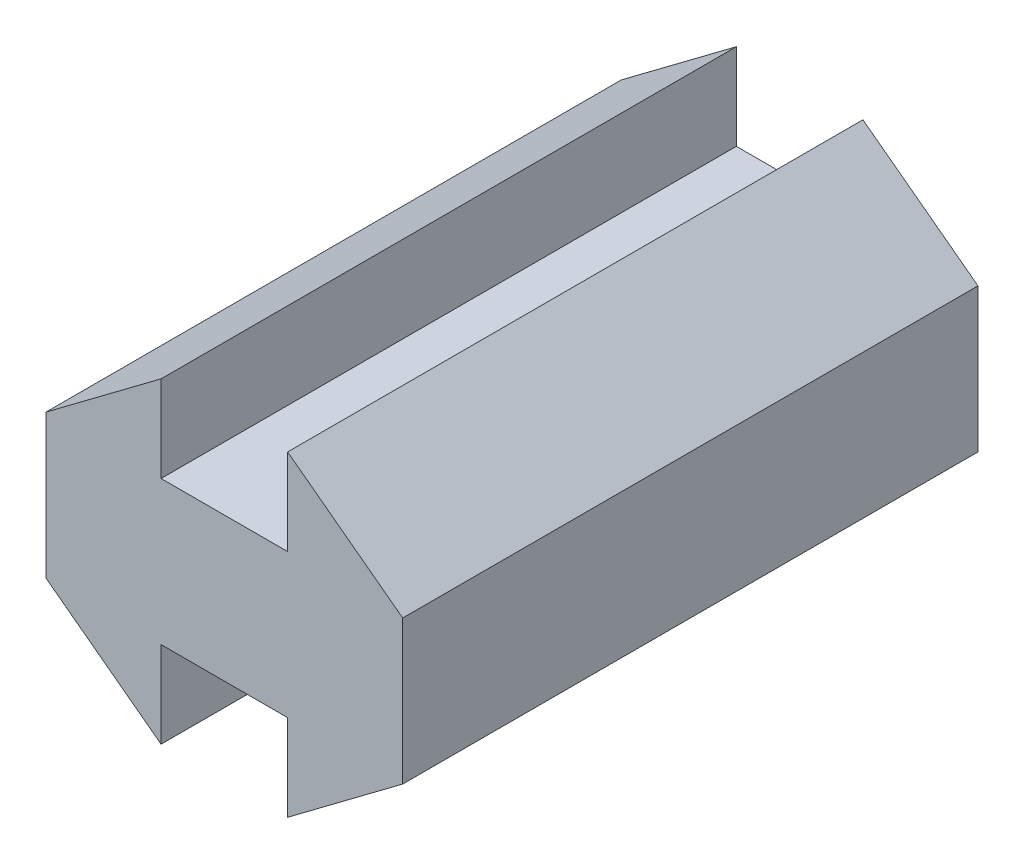
SolidWorks part; units mm, degrees
ref_plane "Plan de face" through (0, 0, 0) normal (0, 0, 1) x (1, 0, 0)
ref_plane "Plan de dessus" through (0, 0, 0) normal (0, 1, 0) x (1, 0, 0)
ref_plane "Plan de droite" through (0, 0, 0) normal (1, 0, 0) x (0, 0, -1)
sketch "ProfileRainureEsquisse" plane through (0, 0, 0) normal (0, 0, 1) x (1, 0, 0)
  line L0 (0, 0) -> (0, 5)
  line L1 (0, 5) -> (4, 8)
  line L2 (0, 0) -> (4, -3)
  line L3 (4, 8) -> (4, 5)
  line L4 (4, 5) -> (8.4, 5)
  line L5 (8.4, 0) -> (8.4, -3)
  line L6 (8.4, 0) -> (4, 0)
  line L7 (4, 0) -> (4, -3)
  line L8 (8.4, 5) -> (8.4, 8)
  line L11 (8.4, 8) -> (12.4, 5)
  line L12 (12.4, 5) -> (12.4, 0)
  line L13 (12.4, 0) -> (8.4, -3)
  point P4 (0, 2.5)
  point P14 (10.4, 2.5)
  dimension "D1" = 4
  dimension "D2" = 4.4
  dimension "D3" = 5
  dimension "D4" = 8
extrude "Boss.-Extru.1" add sketch "ProfileRainureEsquisse" along normal blind 20
